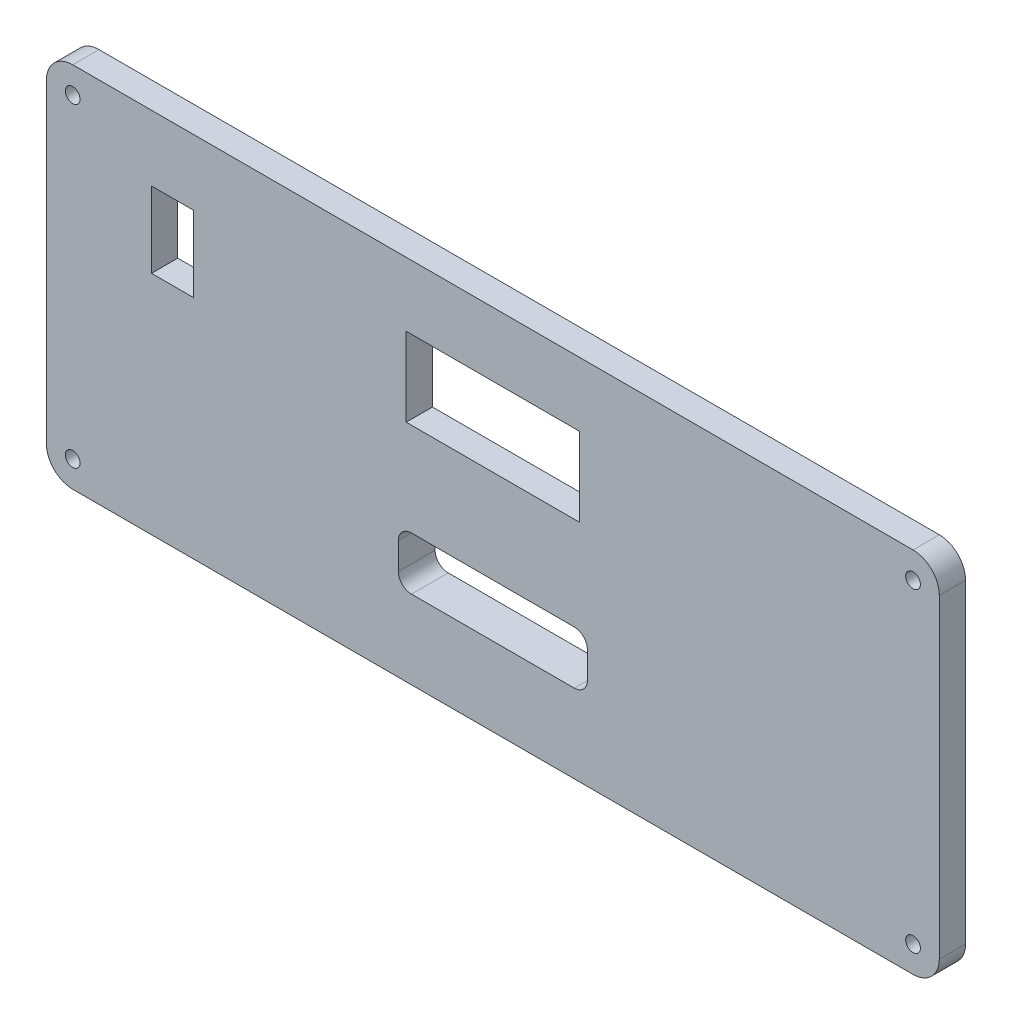
SolidWorks part; units mm, degrees
ref_plane "Front Plane" through (0, 0, 0) normal (0, 0, 1) x (1, 0, 0)
ref_plane "Top Plane" through (0, 0, 0) normal (0, 1, 0) x (1, 0, 0)
ref_plane "Right Plane" through (0, 0, 0) normal (1, 0, 0) x (0, 0, -1)
sketch "Sketch1" plane through (0, 0, 0) normal (0, 0, 1) x (1, 0, 0)
  line L1 (-85, 35) -> (85, 35)
  line L2 (-85, 35) -> (-85, -35)
  line L3 (-85, -35) -> (85, -35)
  line L4 (85, 35) -> (85, -35)
  line L5 (-85, 35) -> (85, -35) construction
  line L6 (-85, -35) -> (85, 35) construction
  point P0 (0, 0)
  dimension "D1" = 170
  dimension "D2" = 70
extrude "Boss-Extrude1" add sketch "Sketch1" along normal blind 5
fillet "Fillet2" radius 5 4 edges at (-85, 35, 2.5) (-85, -35, 2.5) (85, -35, 2.5) (85, 35, 2.5)
sketch "Sketch3" plane through (0, 0, 0) normal (0, 0, 1) x (1, 0, 0)
  circle A0 centre (-80, 30) radius 1.4
  dimension "D1" = 2.8
extrude "Cut-Extrude1" cut sketch "Sketch3" along normal blind 5
sketch "Sketch5" plane through (0, 0, 5) normal (0, 0, 1) x (1, 0, 0)
  circle A1 centre (-80, -30) radius 1.4
  circle A2 centre (80, 30) radius 1.4
  circle A4 centre (80, -30) radius 1.4
  dimension "D1" = 2.8
  dimension "D2" = 2.8
  dimension "D3" = 2.8
extrude "Cut-Extrude2" cut sketch "Sketch5" against normal blind 5
sketch "Sketch6" plane through (0, 0, 0) normal (0, 0, 1) x (1, 0, 0)
  line L5 (0, 7.8069) -> (16.5, 7.8069)
  line L6 (16.5, 7.8069) -> (16.5, 22.8069)
  line L7 (0, 7.8069) -> (-16.5, 7.8069)
  line L8 (-16.5, 7.8069) -> (-16.5, 22.8069)
  line L9 (-16.5, 22.8069) -> (16.5, 22.8069)
  dimension "D1" = 16.5
  dimension "D2" = 33
extrude "Cut-Extrude5" cut sketch "Sketch6" along normal blind 5 contours L7 L8 L9 L6 L5
sketch "Sketch7" plane through (0, 0, 0) normal (0, 0, 1) x (1, 0, 0)
  line L3 (-65, 15.3069) -> (-65, 22.5069)
  line L4 (-65, 22.5069) -> (-57, 22.5069)
  line L5 (-57, 22.5069) -> (-57, 15.3069)
  line L6 (-57, 15.3069) -> (-57, 8.1069)
  line L7 (-57, 8.1069) -> (-65, 8.1069)
  line L8 (-65, 8.1069) -> (-65, 15.3069)
  dimension "D2" = 7.2
  dimension "D3" = 7.2
  dimension "D4" = 8
extrude "Cut-Extrude7" cut sketch "Sketch7" along normal blind 5
sketch "Sketch8" plane through (0, 0, 5) normal (0, 0, 1) x (1, 0, 0)
  line L6 (0, -2) -> (28.5, -2)
  line L7 (28.5, -2) -> (28.5, -14.1531)
  line L9 (-28.5, -14.1531) -> (-28.5, -2)
  line L10 (-28.5, -2) -> (0, -2)
  line L11 (-28.5, -14.1531) -> (-28.5, -28)
  line L12 (-28.5, -28) -> (28.5, -28)
  line L13 (28.5, -28) -> (28.5, -14.1531)
  dimension "D1" = 28.5
  dimension "D2" = 28.5
  dimension "D4" = 26
extrude "Boss-Extrude2" add sketch "Sketch8" against normal blind 10
sketch "Sketch9" plane through (0, 0, -5) normal (0, 0, -1) x (-1, 0, 0)
  line L1 (18, -20.04) -> (-18, -20.04)
  line L7 (18, -9.96) -> (-18, -9.96)
  line L11 (-18, -9.96) -> (-18, -15)
  line L12 (-18, -15) -> (-18, -20.04)
  line L15 (18, -20.04) -> (18, -15)
  line L16 (18, -15) -> (18, -9.96)
extrude "Cut-Extrude8" cut sketch "Sketch9" against normal blind 10
sketch "Sketch10" plane through (28.5, 0, 0) normal (1, 0, 0) x (0, 0, -1)
  line L0 (5, -2) -> (2, -2)
  line L1 (5, -2) -> (0, -2) construction
  line L2 (2, -2) -> (2, -28)
  line L3 (5, -28) -> (0, -28) construction
  line L4 (2, -28) -> (5, -28)
  line L5 (5, -28) -> (5, -2)
extrude "Cut-Extrude9" cut sketch "Sketch10" against normal blind 57
fillet "Fillet3" radius 2.5 4 edges at (18, -20.04, 1.5) (18, -9.96, 1.5) (-18, -9.96, 1.5) (-18, -20.04, 1.5)
